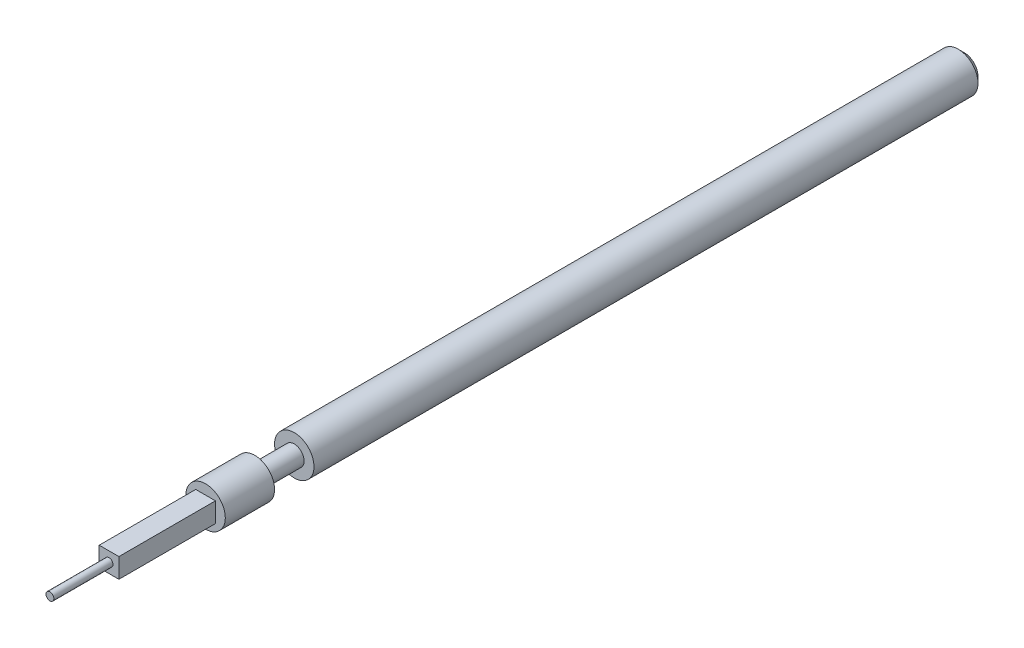
SolidWorks part; units mm, degrees
ref_plane "Alzado" through (0, 0, 0) normal (0, 0, 1) x (1, 0, 0)
ref_plane "Planta" through (0, 0, 0) normal (0, 1, 0) x (1, 0, 0)
ref_plane "Vista lateral" through (0, 0, 0) normal (1, 0, 0) x (0, 0, -1)
sketch "Croquis1" plane through (0, 0, 0) normal (0, 0, 1) x (1, 0, 0)
  circle A0 centre (0, 0) radius 0.5
  dimension "D1" = 1
extrude "Saliente-Extruir1" add sketch "Croquis1" along normal blind 17
cosmetic thread "Rosca cosmética1" parameters "D1"=1.85, "D2"=0.75
chamfer "Chaflán1" distance 0.15 angle 45 1 edges at (0.5, 0, 0)
sketch "Croquis6" plane through (0, 0, 17) normal (0, 0, 1) x (1, 0, 0)
  circle A0 centre (0, 0) radius 0.25
  dimension "D1" = 0.5
extrude "Saliente-Extruir2" add sketch "Croquis6" along normal blind 1
sketch "Croquis7" plane through (0, 0, 18) normal (0, 0, 1) x (1, 0, 0)
  circle A1 centre (0, 0) radius 0.5
  circle A2 centre (0, 0) radius 0.25 construction
  dimension "D1" = 1
extrude "Saliente-Extruir3" add sketch "Croquis7" along normal blind 1.25
sketch "Croquis8" plane through (0, 0, 19.25) normal (0, 0, 1) x (1, 0, 0)
  line L1 (-0.25, 0.25) -> (0.25, 0.25)
  line L2 (-0.25, 0.25) -> (-0.25, -0.25)
  line L3 (-0.25, -0.25) -> (0.25, -0.25)
  line L4 (0.25, 0.25) -> (0.25, -0.25)
  circle A1 centre (0, 0) radius 0.5 construction
  point P4 (0, 0.25)
  point P5 (0, 0)
  point P8 (0.25, 0)
  dimension "D1" = 0.5
extrude "Saliente-Extruir4" add sketch "Croquis8" along normal blind 2.45
sketch "Croquis9" plane through (0, 0, 21.7) normal (0, 0, 1) x (1, 0, 0)
  circle A0 centre (0, 0) radius 0.1
  dimension "D1" = 0.2
extrude "Saliente-Extruir5" add sketch "Croquis9" along normal blind 1.5
